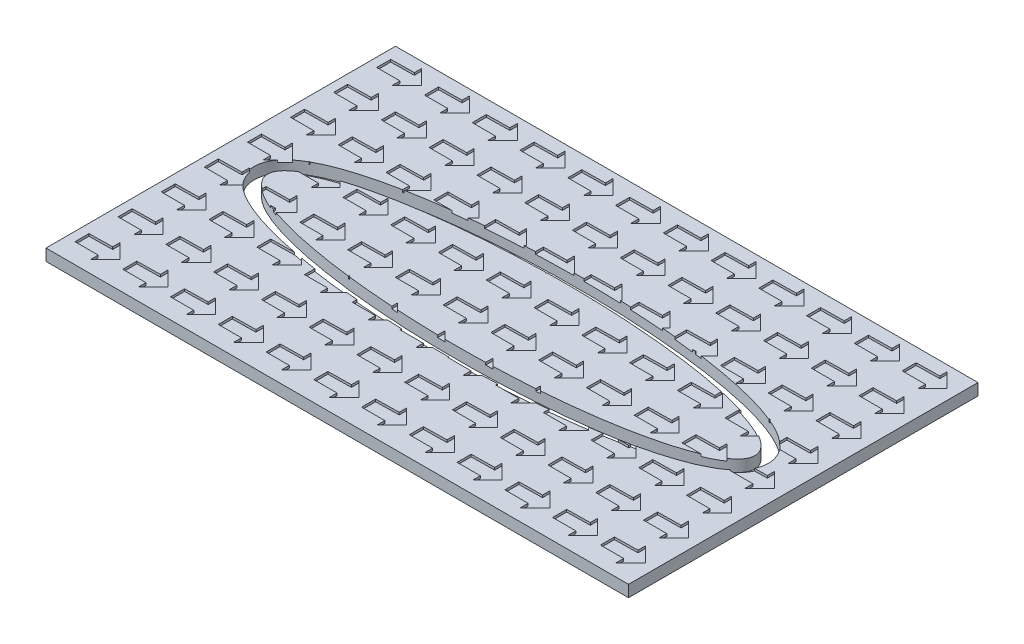
SolidWorks part; units mm, degrees
ref_plane "Front Plane" through (0, 0, 0) normal (0, 0, 1) x (1, 0, 0)
ref_plane "Top Plane" through (0, 0, 0) normal (0, 1, 0) x (1, 0, 0)
ref_plane "Right Plane" through (0, 0, 0) normal (1, 0, 0) x (0, 0, -1)
sketch "Sketch1" plane through (0, 0, 0) normal (0, 1, 0) x (1, 0, 0)
  line L1 (0, 0) -> (250, 0)
  line L2 (0, 0) -> (0, 150)
  line L3 (0, 150) -> (250, 150)
  line L4 (250, 0) -> (250, 150)
extrude "Boss-Extrude1" add sketch "Sketch1" along normal blind 5
sketch "Sketch2" plane through (0, 5, 0) normal (0, 1, 0) x (1, 0, 0)
  ellipse E0 centre (124.7013, 75) end of major axis (229.3097, 75) minor radius 23.3104
  spline S1 degree 3 poles (15.0926, 79.7899) (13.9648, 75) (15.0926, 70.2101) (17.6775, 66.4979) (21.0677, 63.529) (25.2033, 60.971) (30.1026, 58.6696) (37.6668, 55.8618) (49.0289, 52.785) (65.3757, 49.7981) (83.8897, 47.5943) (103.9101, 46.2414) (124.7013, 45.7853) (145.4926, 46.2414) (165.513, 47.5943) (184.027, 49.7981) (200.3738, 52.785) (211.7359, 55.8618) (219.3001, 58.6696) (224.1993, 60.971) (228.335, 63.529) (231.7252, 66.4979) (234.3101, 70.2101) (235.4379, 75) (234.3101, 79.7899) (231.7252, 83.5021) (228.335, 86.471) (224.1993, 89.029) (219.3001, 91.3304) (211.7359, 94.1382) (200.3738, 97.215) (184.027, 100.2019) (165.513, 102.4057) (145.4926, 103.7586) (124.7013, 104.2147) (103.9101, 103.7586) (83.8897, 102.4057) (65.3757, 100.2019) (49.0289, 97.215) (37.6668, 94.1382) (30.1026, 91.3304) (25.2033, 89.029) (21.0677, 86.471) (17.6775, 83.5021) (15.0926, 79.7899) (13.9648, 75) (15.0926, 70.2101) knots -0.294524 -0.19635 -0.098175 0 0.098175 0.19635 0.294524 0.392699 0.490874 0.589049 0.785398 0.981748 1.178097 1.374447 1.570796 1.767146 1.963495 2.159845 2.356194 2.552544 2.650719 2.748894 2.847068 2.945243 3.043418 3.141593 3.239767 3.337942 3.436117 3.534292 3.632467 3.730641 3.926991 4.12334 4.31969 4.516039 4.712389 4.908739 5.105088 5.301438 5.497787 5.694137 5.792311 5.890486 5.988661 6.086836 6.185011 6.283185 6.38136 6.479535 6.57771 only from (14.3407, 75) to (14.3407, 75)
extrude "Cut-Extrude1" cut sketch "Sketch2" against normal blind 5
sketch "Sketch3" plane through (0, 5, 0) normal (0, 1, 0) x (1, 0, 0)
  line L0 (3.8723, 144.0873) -> (3.8723, 138.0725)
  line L1 (3.8723, 138.0725) -> (13.8442, 138.0725)
  line L2 (13.8442, 138.0725) -> (13.8442, 134.7485)
  line L3 (13.8442, 134.7485) -> (20.1756, 141.0799)
  line L4 (20.1756, 141.0799) -> (13.8442, 147.4113)
  line L5 (13.8442, 147.4113) -> (13.8442, 144.2456)
  line L6 (13.8442, 144.2456) -> (3.8723, 144.0873)
  line L7 (24.3723, 144.0873) -> (24.3723, 138.0725)
  line L8 (24.3723, 138.0725) -> (34.3442, 138.0725)
  line L9 (34.3442, 138.0725) -> (34.3442, 134.7485)
  line L10 (34.3442, 134.7485) -> (40.6756, 141.0799)
  line L11 (40.6756, 141.0799) -> (34.3442, 147.4113)
  line L12 (34.3442, 147.4113) -> (34.3442, 144.2456)
  line L13 (34.3442, 144.2456) -> (24.3723, 144.0873)
  line L14 (44.8723, 144.0873) -> (44.8723, 138.0725)
  line L15 (44.8723, 138.0725) -> (54.8442, 138.0725)
  line L16 (54.8442, 138.0725) -> (54.8442, 134.7485)
  line L17 (54.8442, 134.7485) -> (61.1756, 141.0799)
  line L18 (61.1756, 141.0799) -> (54.8442, 147.4113)
  line L19 (54.8442, 147.4113) -> (54.8442, 144.2456)
  line L20 (54.8442, 144.2456) -> (44.8723, 144.0873)
  line L21 (65.3723, 144.0873) -> (65.3723, 138.0725)
  line L22 (65.3723, 138.0725) -> (75.3442, 138.0725)
  line L23 (75.3442, 138.0725) -> (75.3442, 134.7485)
  line L24 (75.3442, 134.7485) -> (81.6756, 141.0799)
  line L25 (81.6756, 141.0799) -> (75.3442, 147.4113)
  line L26 (75.3442, 147.4113) -> (75.3442, 144.2456)
  line L27 (75.3442, 144.2456) -> (65.3723, 144.0873)
  line L28 (85.8723, 144.0873) -> (85.8723, 138.0725)
  line L29 (85.8723, 138.0725) -> (95.8442, 138.0725)
  line L30 (95.8442, 138.0725) -> (95.8442, 134.7485)
  line L31 (95.8442, 134.7485) -> (102.1756, 141.0799)
  line L32 (102.1756, 141.0799) -> (95.8442, 147.4113)
  line L33 (95.8442, 147.4113) -> (95.8442, 144.2456)
  line L34 (95.8442, 144.2456) -> (85.8723, 144.0873)
  line L35 (106.3723, 144.0873) -> (106.3723, 138.0725)
  line L36 (106.3723, 138.0725) -> (116.3442, 138.0725)
  line L37 (116.3442, 138.0725) -> (116.3442, 134.7485)
  line L38 (116.3442, 134.7485) -> (122.6756, 141.0799)
  line L39 (122.6756, 141.0799) -> (116.3442, 147.4113)
  line L40 (116.3442, 147.4113) -> (116.3442, 144.2456)
  line L41 (116.3442, 144.2456) -> (106.3723, 144.0873)
  line L42 (126.8723, 144.0873) -> (126.8723, 138.0725)
  line L43 (126.8723, 138.0725) -> (136.8442, 138.0725)
  line L44 (136.8442, 138.0725) -> (136.8442, 134.7485)
  line L45 (136.8442, 134.7485) -> (143.1756, 141.0799)
  line L46 (143.1756, 141.0799) -> (136.8442, 147.4113)
  line L47 (136.8442, 147.4113) -> (136.8442, 144.2456)
  line L48 (136.8442, 144.2456) -> (126.8723, 144.0873)
  line L49 (147.3723, 144.0873) -> (147.3723, 138.0725)
  line L50 (147.3723, 138.0725) -> (157.3442, 138.0725)
  line L51 (157.3442, 138.0725) -> (157.3442, 134.7485)
  line L52 (157.3442, 134.7485) -> (163.6756, 141.0799)
  line L53 (163.6756, 141.0799) -> (157.3442, 147.4113)
  line L54 (157.3442, 147.4113) -> (157.3442, 144.2456)
  line L55 (157.3442, 144.2456) -> (147.3723, 144.0873)
  line L56 (167.8723, 144.0873) -> (167.8723, 138.0725)
  line L57 (167.8723, 138.0725) -> (177.8442, 138.0725)
  line L58 (177.8442, 138.0725) -> (177.8442, 134.7485)
  line L59 (177.8442, 134.7485) -> (184.1756, 141.0799)
  line L60 (184.1756, 141.0799) -> (177.8442, 147.4113)
  line L61 (177.8442, 147.4113) -> (177.8442, 144.2456)
  line L62 (177.8442, 144.2456) -> (167.8723, 144.0873)
  line L63 (188.3723, 144.0873) -> (188.3723, 138.0725)
  line L64 (188.3723, 138.0725) -> (198.3442, 138.0725)
  line L65 (198.3442, 138.0725) -> (198.3442, 134.7485)
  line L66 (198.3442, 134.7485) -> (204.6756, 141.0799)
  line L67 (204.6756, 141.0799) -> (198.3442, 147.4113)
  line L68 (198.3442, 147.4113) -> (198.3442, 144.2456)
  line L69 (198.3442, 144.2456) -> (188.3723, 144.0873)
  line L70 (208.8723, 144.0873) -> (208.8723, 138.0725)
  line L71 (208.8723, 138.0725) -> (218.8442, 138.0725)
  line L72 (218.8442, 138.0725) -> (218.8442, 134.7485)
  line L73 (218.8442, 134.7485) -> (225.1756, 141.0799)
  line L74 (225.1756, 141.0799) -> (218.8442, 147.4113)
  line L75 (218.8442, 147.4113) -> (218.8442, 144.2456)
  line L76 (218.8442, 144.2456) -> (208.8723, 144.0873)
  line L77 (229.3723, 144.0873) -> (229.3723, 138.0725)
  line L78 (229.3723, 138.0725) -> (239.3442, 138.0725)
  line L79 (239.3442, 138.0725) -> (239.3442, 134.7485)
  line L80 (239.3442, 134.7485) -> (245.6756, 141.0799)
  line L81 (245.6756, 141.0799) -> (239.3442, 147.4113)
  line L82 (239.3442, 147.4113) -> (239.3442, 144.2456)
  line L83 (239.3442, 144.2456) -> (229.3723, 144.0873)
  line L84 (24.3723, 125.5873) -> (24.3723, 119.5725)
  line L85 (24.3723, 119.5725) -> (34.3442, 119.5725)
  line L86 (34.3442, 119.5725) -> (34.3442, 116.2485)
  line L87 (34.3442, 116.2485) -> (40.6756, 122.5799)
  line L88 (40.6756, 122.5799) -> (34.3442, 128.9113)
  line L89 (34.3442, 128.9113) -> (34.3442, 125.7456)
  line L90 (34.3442, 125.7456) -> (24.3723, 125.5873)
  line L91 (44.8723, 125.5873) -> (44.8723, 119.5725)
  line L92 (44.8723, 119.5725) -> (54.8442, 119.5725)
  line L93 (54.8442, 119.5725) -> (54.8442, 116.2485)
  line L94 (54.8442, 116.2485) -> (61.1756, 122.5799)
  line L95 (61.1756, 122.5799) -> (54.8442, 128.9113)
  line L96 (54.8442, 128.9113) -> (54.8442, 125.7456)
  line L97 (54.8442, 125.7456) -> (44.8723, 125.5873)
  line L98 (65.3723, 125.5873) -> (65.3723, 119.5725)
  line L99 (65.3723, 119.5725) -> (75.3442, 119.5725)
  line L100 (75.3442, 119.5725) -> (75.3442, 116.2485)
  line L101 (75.3442, 116.2485) -> (81.6756, 122.5799)
  line L102 (81.6756, 122.5799) -> (75.3442, 128.9113)
  line L103 (75.3442, 128.9113) -> (75.3442, 125.7456)
  line L104 (75.3442, 125.7456) -> (65.3723, 125.5873)
  line L105 (85.8723, 125.5873) -> (85.8723, 119.5725)
  line L106 (85.8723, 119.5725) -> (95.8442, 119.5725)
  line L107 (95.8442, 119.5725) -> (95.8442, 116.2485)
  line L108 (95.8442, 116.2485) -> (102.1756, 122.5799)
  line L109 (102.1756, 122.5799) -> (95.8442, 128.9113)
  line L110 (95.8442, 128.9113) -> (95.8442, 125.7456)
  line L111 (95.8442, 125.7456) -> (85.8723, 125.5873)
  line L112 (106.3723, 125.5873) -> (106.3723, 119.5725)
  line L113 (106.3723, 119.5725) -> (116.3442, 119.5725)
  line L114 (116.3442, 119.5725) -> (116.3442, 116.2485)
  line L115 (116.3442, 116.2485) -> (122.6756, 122.5799)
  line L116 (122.6756, 122.5799) -> (116.3442, 128.9113)
  line L117 (116.3442, 128.9113) -> (116.3442, 125.7456)
  line L118 (116.3442, 125.7456) -> (106.3723, 125.5873)
  line L119 (126.8723, 125.5873) -> (126.8723, 119.5725)
  line L120 (126.8723, 119.5725) -> (136.8442, 119.5725)
  line L121 (136.8442, 119.5725) -> (136.8442, 116.2485)
  line L122 (136.8442, 116.2485) -> (143.1756, 122.5799)
  line L123 (143.1756, 122.5799) -> (136.8442, 128.9113)
  line L124 (136.8442, 128.9113) -> (136.8442, 125.7456)
  line L125 (136.8442, 125.7456) -> (126.8723, 125.5873)
  line L126 (147.3723, 125.5873) -> (147.3723, 119.5725)
  line L127 (147.3723, 119.5725) -> (157.3442, 119.5725)
  line L128 (157.3442, 119.5725) -> (157.3442, 116.2485)
  line L129 (157.3442, 116.2485) -> (163.6756, 122.5799)
  line L130 (163.6756, 122.5799) -> (157.3442, 128.9113)
  line L131 (157.3442, 128.9113) -> (157.3442, 125.7456)
  line L132 (157.3442, 125.7456) -> (147.3723, 125.5873)
  line L133 (167.8723, 125.5873) -> (167.8723, 119.5725)
  line L134 (167.8723, 119.5725) -> (177.8442, 119.5725)
  line L135 (177.8442, 119.5725) -> (177.8442, 116.2485)
  line L136 (177.8442, 116.2485) -> (184.1756, 122.5799)
  line L137 (184.1756, 122.5799) -> (177.8442, 128.9113)
  line L138 (177.8442, 128.9113) -> (177.8442, 125.7456)
  line L139 (177.8442, 125.7456) -> (167.8723, 125.5873)
  line L140 (188.3723, 125.5873) -> (188.3723, 119.5725)
  line L141 (188.3723, 119.5725) -> (198.3442, 119.5725)
  line L142 (198.3442, 119.5725) -> (198.3442, 116.2485)
  line L143 (198.3442, 116.2485) -> (204.6756, 122.5799)
  line L144 (204.6756, 122.5799) -> (198.3442, 128.9113)
  line L145 (198.3442, 128.9113) -> (198.3442, 125.7456)
  line L146 (198.3442, 125.7456) -> (188.3723, 125.5873)
  line L147 (208.8723, 125.5873) -> (208.8723, 119.5725)
  line L148 (208.8723, 119.5725) -> (218.8442, 119.5725)
  line L149 (218.8442, 119.5725) -> (218.8442, 116.2485)
  line L150 (218.8442, 116.2485) -> (225.1756, 122.5799)
  line L151 (225.1756, 122.5799) -> (218.8442, 128.9113)
  line L152 (218.8442, 128.9113) -> (218.8442, 125.7456)
  line L153 (218.8442, 125.7456) -> (208.8723, 125.5873)
  line L154 (229.3723, 125.5873) -> (229.3723, 119.5725)
  line L155 (229.3723, 119.5725) -> (239.3442, 119.5725)
  line L156 (239.3442, 119.5725) -> (239.3442, 116.2485)
  line L157 (239.3442, 116.2485) -> (245.6756, 122.5799)
  line L158 (245.6756, 122.5799) -> (239.3442, 128.9113)
  line L159 (239.3442, 128.9113) -> (239.3442, 125.7456)
  line L160 (239.3442, 125.7456) -> (229.3723, 125.5873)
  line L161 (24.3723, 107.0873) -> (24.3723, 101.0725)
  line L162 (24.3723, 101.0725) -> (34.3442, 101.0725)
  line L163 (34.3442, 101.0725) -> (34.3442, 97.7485)
  line L164 (34.3442, 97.7485) -> (40.6756, 104.0799)
  line L165 (40.6756, 104.0799) -> (34.3442, 110.4113)
  line L166 (34.3442, 110.4113) -> (34.3442, 107.2456)
  line L167 (34.3442, 107.2456) -> (24.3723, 107.0873)
  line L168 (44.8723, 107.0873) -> (44.8723, 101.0725)
  line L169 (44.8723, 101.0725) -> (54.8442, 101.0725)
  line L170 (54.8442, 101.0725) -> (54.8442, 97.7485)
  line L171 (54.8442, 97.7485) -> (61.1756, 104.0799)
  line L172 (61.1756, 104.0799) -> (54.8442, 110.4113)
  line L173 (54.8442, 110.4113) -> (54.8442, 107.2456)
  line L174 (54.8442, 107.2456) -> (44.8723, 107.0873)
  line L175 (65.3723, 107.0873) -> (65.3723, 101.0725)
  line L176 (65.3723, 101.0725) -> (75.3442, 101.0725)
  line L177 (75.3442, 101.0725) -> (75.3442, 97.7485)
  line L178 (75.3442, 97.7485) -> (81.6756, 104.0799)
  line L179 (81.6756, 104.0799) -> (75.3442, 110.4113)
  line L180 (75.3442, 110.4113) -> (75.3442, 107.2456)
  line L181 (75.3442, 107.2456) -> (65.3723, 107.0873)
  line L182 (85.8723, 107.0873) -> (85.8723, 101.0725)
  line L183 (85.8723, 101.0725) -> (95.8442, 101.0725)
  line L184 (95.8442, 101.0725) -> (95.8442, 97.7485)
  line L185 (95.8442, 97.7485) -> (102.1756, 104.0799)
  line L186 (102.1756, 104.0799) -> (95.8442, 110.4113)
  line L187 (95.8442, 110.4113) -> (95.8442, 107.2456)
  line L188 (95.8442, 107.2456) -> (85.8723, 107.0873)
  line L189 (106.3723, 107.0873) -> (106.3723, 101.0725)
  line L190 (106.3723, 101.0725) -> (116.3442, 101.0725)
  line L191 (116.3442, 101.0725) -> (116.3442, 97.7485)
  line L192 (116.3442, 97.7485) -> (122.6756, 104.0799)
  line L193 (122.6756, 104.0799) -> (116.3442, 110.4113)
  line L194 (116.3442, 110.4113) -> (116.3442, 107.2456)
  line L195 (116.3442, 107.2456) -> (106.3723, 107.0873)
  line L196 (126.8723, 107.0873) -> (126.8723, 101.0725)
  line L197 (126.8723, 101.0725) -> (136.8442, 101.0725)
  line L198 (136.8442, 101.0725) -> (136.8442, 97.7485)
  line L199 (136.8442, 97.7485) -> (143.1756, 104.0799)
  line L200 (143.1756, 104.0799) -> (136.8442, 110.4113)
  line L201 (136.8442, 110.4113) -> (136.8442, 107.2456)
  line L202 (136.8442, 107.2456) -> (126.8723, 107.0873)
  line L203 (147.3723, 107.0873) -> (147.3723, 101.0725)
  line L204 (147.3723, 101.0725) -> (157.3442, 101.0725)
  line L205 (157.3442, 101.0725) -> (157.3442, 97.7485)
  line L206 (157.3442, 97.7485) -> (163.6756, 104.0799)
  line L207 (163.6756, 104.0799) -> (157.3442, 110.4113)
  line L208 (157.3442, 110.4113) -> (157.3442, 107.2456)
  line L209 (157.3442, 107.2456) -> (147.3723, 107.0873)
  line L210 (167.8723, 107.0873) -> (167.8723, 101.0725)
  line L211 (167.8723, 101.0725) -> (177.8442, 101.0725)
  line L212 (177.8442, 101.0725) -> (177.8442, 97.7485)
  line L213 (177.8442, 97.7485) -> (184.1756, 104.0799)
  line L214 (184.1756, 104.0799) -> (177.8442, 110.4113)
  line L215 (177.8442, 110.4113) -> (177.8442, 107.2456)
  line L216 (177.8442, 107.2456) -> (167.8723, 107.0873)
  line L217 (188.3723, 107.0873) -> (188.3723, 101.0725)
  line L218 (188.3723, 101.0725) -> (198.3442, 101.0725)
  line L219 (198.3442, 101.0725) -> (198.3442, 97.7485)
  line L220 (198.3442, 97.7485) -> (204.6756, 104.0799)
  line L221 (204.6756, 104.0799) -> (198.3442, 110.4113)
  line L222 (198.3442, 110.4113) -> (198.3442, 107.2456)
  line L223 (198.3442, 107.2456) -> (188.3723, 107.0873)
  line L224 (208.8723, 107.0873) -> (208.8723, 101.0725)
  line L225 (208.8723, 101.0725) -> (218.8442, 101.0725)
  line L226 (218.8442, 101.0725) -> (218.8442, 97.7485)
  line L227 (218.8442, 97.7485) -> (225.1756, 104.0799)
  line L228 (225.1756, 104.0799) -> (218.8442, 110.4113)
  line L229 (218.8442, 110.4113) -> (218.8442, 107.2456)
  line L230 (218.8442, 107.2456) -> (208.8723, 107.0873)
  line L231 (229.3723, 107.0873) -> (229.3723, 101.0725)
  line L232 (229.3723, 101.0725) -> (239.3442, 101.0725)
  line L233 (239.3442, 101.0725) -> (239.3442, 97.7485)
  line L234 (239.3442, 97.7485) -> (245.6756, 104.0799)
  line L235 (245.6756, 104.0799) -> (239.3442, 110.4113)
  line L236 (239.3442, 110.4113) -> (239.3442, 107.2456)
  line L237 (239.3442, 107.2456) -> (229.3723, 107.0873)
  line L238 (24.3723, 88.5873) -> (24.3723, 82.5725)
  line L239 (24.3723, 82.5725) -> (34.3442, 82.5725)
  line L240 (34.3442, 82.5725) -> (34.3442, 79.2485)
  line L241 (34.3442, 79.2485) -> (40.6756, 85.5799)
  line L242 (40.6756, 85.5799) -> (34.3442, 91.9113)
  line L243 (34.3442, 91.9113) -> (34.3442, 88.7456)
  line L244 (34.3442, 88.7456) -> (24.3723, 88.5873)
  line L245 (44.8723, 88.5873) -> (44.8723, 82.5725)
  line L246 (44.8723, 82.5725) -> (54.8442, 82.5725)
  line L247 (54.8442, 82.5725) -> (54.8442, 79.2485)
  line L248 (54.8442, 79.2485) -> (61.1756, 85.5799)
  line L249 (61.1756, 85.5799) -> (54.8442, 91.9113)
  line L250 (54.8442, 91.9113) -> (54.8442, 88.7456)
  line L251 (54.8442, 88.7456) -> (44.8723, 88.5873)
  line L252 (65.3723, 88.5873) -> (65.3723, 82.5725)
  line L253 (65.3723, 82.5725) -> (75.3442, 82.5725)
  line L254 (75.3442, 82.5725) -> (75.3442, 79.2485)
  line L255 (75.3442, 79.2485) -> (81.6756, 85.5799)
  line L256 (81.6756, 85.5799) -> (75.3442, 91.9113)
  line L257 (75.3442, 91.9113) -> (75.3442, 88.7456)
  line L258 (75.3442, 88.7456) -> (65.3723, 88.5873)
  line L259 (85.8723, 88.5873) -> (85.8723, 82.5725)
  line L260 (85.8723, 82.5725) -> (95.8442, 82.5725)
  line L261 (95.8442, 82.5725) -> (95.8442, 79.2485)
  line L262 (95.8442, 79.2485) -> (102.1756, 85.5799)
  line L263 (102.1756, 85.5799) -> (95.8442, 91.9113)
  line L264 (95.8442, 91.9113) -> (95.8442, 88.7456)
  line L265 (95.8442, 88.7456) -> (85.8723, 88.5873)
  line L266 (106.3723, 88.5873) -> (106.3723, 82.5725)
  line L267 (106.3723, 82.5725) -> (116.3442, 82.5725)
  line L268 (116.3442, 82.5725) -> (116.3442, 79.2485)
  line L269 (116.3442, 79.2485) -> (122.6756, 85.5799)
  line L270 (122.6756, 85.5799) -> (116.3442, 91.9113)
  line L271 (116.3442, 91.9113) -> (116.3442, 88.7456)
  line L272 (116.3442, 88.7456) -> (106.3723, 88.5873)
  line L273 (126.8723, 88.5873) -> (126.8723, 82.5725)
  line L274 (126.8723, 82.5725) -> (136.8442, 82.5725)
  line L275 (136.8442, 82.5725) -> (136.8442, 79.2485)
  line L276 (136.8442, 79.2485) -> (143.1756, 85.5799)
  line L277 (143.1756, 85.5799) -> (136.8442, 91.9113)
  line L278 (136.8442, 91.9113) -> (136.8442, 88.7456)
  line L279 (136.8442, 88.7456) -> (126.8723, 88.5873)
  line L280 (147.3723, 88.5873) -> (147.3723, 82.5725)
  line L281 (147.3723, 82.5725) -> (157.3442, 82.5725)
  line L282 (157.3442, 82.5725) -> (157.3442, 79.2485)
  line L283 (157.3442, 79.2485) -> (163.6756, 85.5799)
  line L284 (163.6756, 85.5799) -> (157.3442, 91.9113)
  line L285 (157.3442, 91.9113) -> (157.3442, 88.7456)
  line L286 (157.3442, 88.7456) -> (147.3723, 88.5873)
  line L287 (167.8723, 88.5873) -> (167.8723, 82.5725)
  line L288 (167.8723, 82.5725) -> (177.8442, 82.5725)
  line L289 (177.8442, 82.5725) -> (177.8442, 79.2485)
  line L290 (177.8442, 79.2485) -> (184.1756, 85.5799)
  line L291 (184.1756, 85.5799) -> (177.8442, 91.9113)
  line L292 (177.8442, 91.9113) -> (177.8442, 88.7456)
  line L293 (177.8442, 88.7456) -> (167.8723, 88.5873)
  line L294 (188.3723, 88.5873) -> (188.3723, 82.5725)
  line L295 (188.3723, 82.5725) -> (198.3442, 82.5725)
  line L296 (198.3442, 82.5725) -> (198.3442, 79.2485)
  line L297 (198.3442, 79.2485) -> (204.6756, 85.5799)
  line L298 (204.6756, 85.5799) -> (198.3442, 91.9113)
  line L299 (198.3442, 91.9113) -> (198.3442, 88.7456)
  line L300 (198.3442, 88.7456) -> (188.3723, 88.5873)
  line L301 (208.8723, 88.5873) -> (208.8723, 82.5725)
  line L302 (208.8723, 82.5725) -> (218.8442, 82.5725)
  line L303 (218.8442, 82.5725) -> (218.8442, 79.2485)
  line L304 (218.8442, 79.2485) -> (225.1756, 85.5799)
  line L305 (225.1756, 85.5799) -> (218.8442, 91.9113)
  line L306 (218.8442, 91.9113) -> (218.8442, 88.7456)
  line L307 (218.8442, 88.7456) -> (208.8723, 88.5873)
  line L308 (229.3723, 88.5873) -> (229.3723, 82.5725)
  line L309 (229.3723, 82.5725) -> (239.3442, 82.5725)
  line L310 (239.3442, 82.5725) -> (239.3442, 79.2485)
  line L311 (239.3442, 79.2485) -> (245.6756, 85.5799)
  line L312 (245.6756, 85.5799) -> (239.3442, 91.9113)
  line L313 (239.3442, 91.9113) -> (239.3442, 88.7456)
  line L314 (239.3442, 88.7456) -> (229.3723, 88.5873)
  line L315 (24.3723, 70.0873) -> (24.3723, 64.0725)
  line L316 (24.3723, 64.0725) -> (34.3442, 64.0725)
  line L317 (34.3442, 64.0725) -> (34.3442, 60.7485)
  line L318 (34.3442, 60.7485) -> (40.6756, 67.0799)
  line L319 (40.6756, 67.0799) -> (34.3442, 73.4113)
  line L320 (34.3442, 73.4113) -> (34.3442, 70.2456)
  line L321 (34.3442, 70.2456) -> (24.3723, 70.0873)
  line L322 (44.8723, 70.0873) -> (44.8723, 64.0725)
  line L323 (44.8723, 64.0725) -> (54.8442, 64.0725)
  line L324 (54.8442, 64.0725) -> (54.8442, 60.7485)
  line L325 (54.8442, 60.7485) -> (61.1756, 67.0799)
  line L326 (61.1756, 67.0799) -> (54.8442, 73.4113)
  line L327 (54.8442, 73.4113) -> (54.8442, 70.2456)
  line L328 (54.8442, 70.2456) -> (44.8723, 70.0873)
  line L329 (65.3723, 70.0873) -> (65.3723, 64.0725)
  line L330 (65.3723, 64.0725) -> (75.3442, 64.0725)
  line L331 (75.3442, 64.0725) -> (75.3442, 60.7485)
  line L332 (75.3442, 60.7485) -> (81.6756, 67.0799)
  line L333 (81.6756, 67.0799) -> (75.3442, 73.4113)
  line L334 (75.3442, 73.4113) -> (75.3442, 70.2456)
  line L335 (75.3442, 70.2456) -> (65.3723, 70.0873)
  line L336 (85.8723, 70.0873) -> (85.8723, 64.0725)
  line L337 (85.8723, 64.0725) -> (95.8442, 64.0725)
  line L338 (95.8442, 64.0725) -> (95.8442, 60.7485)
  line L339 (95.8442, 60.7485) -> (102.1756, 67.0799)
  line L340 (102.1756, 67.0799) -> (95.8442, 73.4113)
  line L341 (95.8442, 73.4113) -> (95.8442, 70.2456)
  line L342 (95.8442, 70.2456) -> (85.8723, 70.0873)
  line L343 (106.3723, 70.0873) -> (106.3723, 64.0725)
  line L344 (106.3723, 64.0725) -> (116.3442, 64.0725)
  line L345 (116.3442, 64.0725) -> (116.3442, 60.7485)
  line L346 (116.3442, 60.7485) -> (122.6756, 67.0799)
  line L347 (122.6756, 67.0799) -> (116.3442, 73.4113)
  line L348 (116.3442, 73.4113) -> (116.3442, 70.2456)
  line L349 (116.3442, 70.2456) -> (106.3723, 70.0873)
  line L350 (126.8723, 70.0873) -> (126.8723, 64.0725)
  line L351 (126.8723, 64.0725) -> (136.8442, 64.0725)
  line L352 (136.8442, 64.0725) -> (136.8442, 60.7485)
  line L353 (136.8442, 60.7485) -> (143.1756, 67.0799)
  line L354 (143.1756, 67.0799) -> (136.8442, 73.4113)
  line L355 (136.8442, 73.4113) -> (136.8442, 70.2456)
  line L356 (136.8442, 70.2456) -> (126.8723, 70.0873)
  line L357 (147.3723, 70.0873) -> (147.3723, 64.0725)
  line L358 (147.3723, 64.0725) -> (157.3442, 64.0725)
  line L359 (157.3442, 64.0725) -> (157.3442, 60.7485)
  line L360 (157.3442, 60.7485) -> (163.6756, 67.0799)
  line L361 (163.6756, 67.0799) -> (157.3442, 73.4113)
  line L362 (157.3442, 73.4113) -> (157.3442, 70.2456)
  line L363 (157.3442, 70.2456) -> (147.3723, 70.0873)
  line L364 (167.8723, 70.0873) -> (167.8723, 64.0725)
  line L365 (167.8723, 64.0725) -> (177.8442, 64.0725)
  line L366 (177.8442, 64.0725) -> (177.8442, 60.7485)
  line L367 (177.8442, 60.7485) -> (184.1756, 67.0799)
  line L368 (184.1756, 67.0799) -> (177.8442, 73.4113)
  line L369 (177.8442, 73.4113) -> (177.8442, 70.2456)
  line L370 (177.8442, 70.2456) -> (167.8723, 70.0873)
  line L371 (188.3723, 70.0873) -> (188.3723, 64.0725)
  line L372 (188.3723, 64.0725) -> (198.3442, 64.0725)
  line L373 (198.3442, 64.0725) -> (198.3442, 60.7485)
  line L374 (198.3442, 60.7485) -> (204.6756, 67.0799)
  line L375 (204.6756, 67.0799) -> (198.3442, 73.4113)
  line L376 (198.3442, 73.4113) -> (198.3442, 70.2456)
  line L377 (198.3442, 70.2456) -> (188.3723, 70.0873)
  line L378 (208.8723, 70.0873) -> (208.8723, 64.0725)
  line L379 (208.8723, 64.0725) -> (218.8442, 64.0725)
  line L380 (218.8442, 64.0725) -> (218.8442, 60.7485)
  line L381 (218.8442, 60.7485) -> (225.1756, 67.0799)
  line L382 (225.1756, 67.0799) -> (218.8442, 73.4113)
  line L383 (218.8442, 73.4113) -> (218.8442, 70.2456)
  line L384 (218.8442, 70.2456) -> (208.8723, 70.0873)
  line L385 (229.3723, 70.0873) -> (229.3723, 64.0725)
  line L386 (229.3723, 64.0725) -> (239.3442, 64.0725)
  line L387 (239.3442, 64.0725) -> (239.3442, 60.7485)
  line L388 (239.3442, 60.7485) -> (245.6756, 67.0799)
  line L389 (245.6756, 67.0799) -> (239.3442, 73.4113)
  line L390 (239.3442, 73.4113) -> (239.3442, 70.2456)
  line L391 (239.3442, 70.2456) -> (229.3723, 70.0873)
  line L392 (24.3723, 51.5873) -> (24.3723, 45.5725)
  line L393 (24.3723, 45.5725) -> (34.3442, 45.5725)
  line L394 (34.3442, 45.5725) -> (34.3442, 42.2485)
  line L395 (34.3442, 42.2485) -> (40.6756, 48.5799)
  line L396 (40.6756, 48.5799) -> (34.3442, 54.9113)
  line L397 (34.3442, 54.9113) -> (34.3442, 51.7456)
  line L398 (34.3442, 51.7456) -> (24.3723, 51.5873)
  line L399 (44.8723, 51.5873) -> (44.8723, 45.5725)
  line L400 (44.8723, 45.5725) -> (54.8442, 45.5725)
  line L401 (54.8442, 45.5725) -> (54.8442, 42.2485)
  line L402 (54.8442, 42.2485) -> (61.1756, 48.5799)
  line L403 (61.1756, 48.5799) -> (54.8442, 54.9113)
  line L404 (54.8442, 54.9113) -> (54.8442, 51.7456)
  line L405 (54.8442, 51.7456) -> (44.8723, 51.5873)
  line L406 (65.3723, 51.5873) -> (65.3723, 45.5725)
  line L407 (65.3723, 45.5725) -> (75.3442, 45.5725)
  line L408 (75.3442, 45.5725) -> (75.3442, 42.2485)
  line L409 (75.3442, 42.2485) -> (81.6756, 48.5799)
  line L410 (81.6756, 48.5799) -> (75.3442, 54.9113)
  line L411 (75.3442, 54.9113) -> (75.3442, 51.7456)
  line L412 (75.3442, 51.7456) -> (65.3723, 51.5873)
  line L413 (85.8723, 51.5873) -> (85.8723, 45.5725)
  line L414 (85.8723, 45.5725) -> (95.8442, 45.5725)
  line L415 (95.8442, 45.5725) -> (95.8442, 42.2485)
  line L416 (95.8442, 42.2485) -> (102.1756, 48.5799)
  line L417 (102.1756, 48.5799) -> (95.8442, 54.9113)
  line L418 (95.8442, 54.9113) -> (95.8442, 51.7456)
  line L419 (95.8442, 51.7456) -> (85.8723, 51.5873)
  line L420 (106.3723, 51.5873) -> (106.3723, 45.5725)
  line L421 (106.3723, 45.5725) -> (116.3442, 45.5725)
  line L422 (116.3442, 45.5725) -> (116.3442, 42.2485)
  line L423 (116.3442, 42.2485) -> (122.6756, 48.5799)
  line L424 (122.6756, 48.5799) -> (116.3442, 54.9113)
  line L425 (116.3442, 54.9113) -> (116.3442, 51.7456)
  line L426 (116.3442, 51.7456) -> (106.3723, 51.5873)
  line L427 (126.8723, 51.5873) -> (126.8723, 45.5725)
  line L428 (126.8723, 45.5725) -> (136.8442, 45.5725)
  line L429 (136.8442, 45.5725) -> (136.8442, 42.2485)
  line L430 (136.8442, 42.2485) -> (143.1756, 48.5799)
  line L431 (143.1756, 48.5799) -> (136.8442, 54.9113)
  line L432 (136.8442, 54.9113) -> (136.8442, 51.7456)
  line L433 (136.8442, 51.7456) -> (126.8723, 51.5873)
  line L434 (147.3723, 51.5873) -> (147.3723, 45.5725)
  line L435 (147.3723, 45.5725) -> (157.3442, 45.5725)
  line L436 (157.3442, 45.5725) -> (157.3442, 42.2485)
  line L437 (157.3442, 42.2485) -> (163.6756, 48.5799)
  line L438 (163.6756, 48.5799) -> (157.3442, 54.9113)
  line L439 (157.3442, 54.9113) -> (157.3442, 51.7456)
  line L440 (157.3442, 51.7456) -> (147.3723, 51.5873)
  line L441 (167.8723, 51.5873) -> (167.8723, 45.5725)
  line L442 (167.8723, 45.5725) -> (177.8442, 45.5725)
  line L443 (177.8442, 45.5725) -> (177.8442, 42.2485)
  line L444 (177.8442, 42.2485) -> (184.1756, 48.5799)
  line L445 (184.1756, 48.5799) -> (177.8442, 54.9113)
  line L446 (177.8442, 54.9113) -> (177.8442, 51.7456)
  line L447 (177.8442, 51.7456) -> (167.8723, 51.5873)
  line L448 (188.3723, 51.5873) -> (188.3723, 45.5725)
  line L449 (188.3723, 45.5725) -> (198.3442, 45.5725)
  line L450 (198.3442, 45.5725) -> (198.3442, 42.2485)
  line L451 (198.3442, 42.2485) -> (204.6756, 48.5799)
  line L452 (204.6756, 48.5799) -> (198.3442, 54.9113)
  line L453 (198.3442, 54.9113) -> (198.3442, 51.7456)
  line L454 (198.3442, 51.7456) -> (188.3723, 51.5873)
  line L455 (208.8723, 51.5873) -> (208.8723, 45.5725)
  line L456 (208.8723, 45.5725) -> (218.8442, 45.5725)
  line L457 (218.8442, 45.5725) -> (218.8442, 42.2485)
  line L458 (218.8442, 42.2485) -> (225.1756, 48.5799)
  line L459 (225.1756, 48.5799) -> (218.8442, 54.9113)
  line L460 (218.8442, 54.9113) -> (218.8442, 51.7456)
  line L461 (218.8442, 51.7456) -> (208.8723, 51.5873)
  line L462 (229.3723, 51.5873) -> (229.3723, 45.5725)
  line L463 (229.3723, 45.5725) -> (239.3442, 45.5725)
  line L464 (239.3442, 45.5725) -> (239.3442, 42.2485)
  line L465 (239.3442, 42.2485) -> (245.6756, 48.5799)
  line L466 (245.6756, 48.5799) -> (239.3442, 54.9113)
  line L467 (239.3442, 54.9113) -> (239.3442, 51.7456)
  line L468 (239.3442, 51.7456) -> (229.3723, 51.5873)
  line L469 (24.3723, 33.0873) -> (24.3723, 27.0725)
  line L470 (24.3723, 27.0725) -> (34.3442, 27.0725)
  line L471 (34.3442, 27.0725) -> (34.3442, 23.7485)
  line L472 (34.3442, 23.7485) -> (40.6756, 30.0799)
  line L473 (40.6756, 30.0799) -> (34.3442, 36.4113)
  line L474 (34.3442, 36.4113) -> (34.3442, 33.2456)
  line L475 (34.3442, 33.2456) -> (24.3723, 33.0873)
  line L476 (44.8723, 33.0873) -> (44.8723, 27.0725)
  line L477 (44.8723, 27.0725) -> (54.8442, 27.0725)
  line L478 (54.8442, 27.0725) -> (54.8442, 23.7485)
  line L479 (54.8442, 23.7485) -> (61.1756, 30.0799)
  line L480 (61.1756, 30.0799) -> (54.8442, 36.4113)
  line L481 (54.8442, 36.4113) -> (54.8442, 33.2456)
  line L482 (54.8442, 33.2456) -> (44.8723, 33.0873)
  line L483 (65.3723, 33.0873) -> (65.3723, 27.0725)
  line L484 (65.3723, 27.0725) -> (75.3442, 27.0725)
  line L485 (75.3442, 27.0725) -> (75.3442, 23.7485)
  line L486 (75.3442, 23.7485) -> (81.6756, 30.0799)
  line L487 (81.6756, 30.0799) -> (75.3442, 36.4113)
  line L488 (75.3442, 36.4113) -> (75.3442, 33.2456)
  line L489 (75.3442, 33.2456) -> (65.3723, 33.0873)
  line L490 (85.8723, 33.0873) -> (85.8723, 27.0725)
  line L491 (85.8723, 27.0725) -> (95.8442, 27.0725)
  line L492 (95.8442, 27.0725) -> (95.8442, 23.7485)
  line L493 (95.8442, 23.7485) -> (102.1756, 30.0799)
  line L494 (102.1756, 30.0799) -> (95.8442, 36.4113)
  line L495 (95.8442, 36.4113) -> (95.8442, 33.2456)
  line L496 (95.8442, 33.2456) -> (85.8723, 33.0873)
  line L497 (106.3723, 33.0873) -> (106.3723, 27.0725)
  line L498 (106.3723, 27.0725) -> (116.3442, 27.0725)
  line L499 (116.3442, 27.0725) -> (116.3442, 23.7485)
  line L500 (116.3442, 23.7485) -> (122.6756, 30.0799)
  line L501 (122.6756, 30.0799) -> (116.3442, 36.4113)
  line L502 (116.3442, 36.4113) -> (116.3442, 33.2456)
  line L503 (116.3442, 33.2456) -> (106.3723, 33.0873)
  line L504 (126.8723, 33.0873) -> (126.8723, 27.0725)
  line L505 (126.8723, 27.0725) -> (136.8442, 27.0725)
  line L506 (136.8442, 27.0725) -> (136.8442, 23.7485)
  line L507 (136.8442, 23.7485) -> (143.1756, 30.0799)
  line L508 (143.1756, 30.0799) -> (136.8442, 36.4113)
  line L509 (136.8442, 36.4113) -> (136.8442, 33.2456)
  line L510 (136.8442, 33.2456) -> (126.8723, 33.0873)
  line L511 (147.3723, 33.0873) -> (147.3723, 27.0725)
  line L512 (147.3723, 27.0725) -> (157.3442, 27.0725)
  line L513 (157.3442, 27.0725) -> (157.3442, 23.7485)
  line L514 (157.3442, 23.7485) -> (163.6756, 30.0799)
  line L515 (163.6756, 30.0799) -> (157.3442, 36.4113)
  line L516 (157.3442, 36.4113) -> (157.3442, 33.2456)
  line L517 (157.3442, 33.2456) -> (147.3723, 33.0873)
  line L518 (167.8723, 33.0873) -> (167.8723, 27.0725)
  line L519 (167.8723, 27.0725) -> (177.8442, 27.0725)
  line L520 (177.8442, 27.0725) -> (177.8442, 23.7485)
  line L521 (177.8442, 23.7485) -> (184.1756, 30.0799)
  line L522 (184.1756, 30.0799) -> (177.8442, 36.4113)
  line L523 (177.8442, 36.4113) -> (177.8442, 33.2456)
  line L524 (177.8442, 33.2456) -> (167.8723, 33.0873)
  line L525 (188.3723, 33.0873) -> (188.3723, 27.0725)
  line L526 (188.3723, 27.0725) -> (198.3442, 27.0725)
  line L527 (198.3442, 27.0725) -> (198.3442, 23.7485)
  line L528 (198.3442, 23.7485) -> (204.6756, 30.0799)
  line L529 (204.6756, 30.0799) -> (198.3442, 36.4113)
  line L530 (198.3442, 36.4113) -> (198.3442, 33.2456)
  line L531 (198.3442, 33.2456) -> (188.3723, 33.0873)
  line L532 (208.8723, 33.0873) -> (208.8723, 27.0725)
  line L533 (208.8723, 27.0725) -> (218.8442, 27.0725)
  line L534 (218.8442, 27.0725) -> (218.8442, 23.7485)
  line L535 (218.8442, 23.7485) -> (225.1756, 30.0799)
  line L536 (225.1756, 30.0799) -> (218.8442, 36.4113)
  line L537 (218.8442, 36.4113) -> (218.8442, 33.2456)
  line L538 (218.8442, 33.2456) -> (208.8723, 33.0873)
  line L539 (229.3723, 33.0873) -> (229.3723, 27.0725)
  line L540 (229.3723, 27.0725) -> (239.3442, 27.0725)
  line L541 (239.3442, 27.0725) -> (239.3442, 23.7485)
  line L542 (239.3442, 23.7485) -> (245.6756, 30.0799)
  line L543 (245.6756, 30.0799) -> (239.3442, 36.4113)
  line L544 (239.3442, 36.4113) -> (239.3442, 33.2456)
  line L545 (239.3442, 33.2456) -> (229.3723, 33.0873)
  line L546 (24.3723, 14.5873) -> (24.3723, 8.5725)
  line L547 (24.3723, 8.5725) -> (34.3442, 8.5725)
  line L548 (34.3442, 8.5725) -> (34.3442, 5.2485)
  line L549 (34.3442, 5.2485) -> (40.6756, 11.5799)
  line L550 (40.6756, 11.5799) -> (34.3442, 17.9113)
  line L551 (34.3442, 17.9113) -> (34.3442, 14.7456)
  line L552 (34.3442, 14.7456) -> (24.3723, 14.5873)
  line L553 (44.8723, 14.5873) -> (44.8723, 8.5725)
  line L554 (44.8723, 8.5725) -> (54.8442, 8.5725)
  line L555 (54.8442, 8.5725) -> (54.8442, 5.2485)
  line L556 (54.8442, 5.2485) -> (61.1756, 11.5799)
  line L557 (61.1756, 11.5799) -> (54.8442, 17.9113)
  line L558 (54.8442, 17.9113) -> (54.8442, 14.7456)
  line L559 (54.8442, 14.7456) -> (44.8723, 14.5873)
  line L560 (65.3723, 14.5873) -> (65.3723, 8.5725)
  line L561 (65.3723, 8.5725) -> (75.3442, 8.5725)
  line L562 (75.3442, 8.5725) -> (75.3442, 5.2485)
  line L563 (75.3442, 5.2485) -> (81.6756, 11.5799)
  line L564 (81.6756, 11.5799) -> (75.3442, 17.9113)
  line L565 (75.3442, 17.9113) -> (75.3442, 14.7456)
  line L566 (75.3442, 14.7456) -> (65.3723, 14.5873)
  line L567 (85.8723, 14.5873) -> (85.8723, 8.5725)
  line L568 (85.8723, 8.5725) -> (95.8442, 8.5725)
  line L569 (95.8442, 8.5725) -> (95.8442, 5.2485)
  line L570 (95.8442, 5.2485) -> (102.1756, 11.5799)
  line L571 (102.1756, 11.5799) -> (95.8442, 17.9113)
  line L572 (95.8442, 17.9113) -> (95.8442, 14.7456)
  line L573 (95.8442, 14.7456) -> (85.8723, 14.5873)
  line L574 (106.3723, 14.5873) -> (106.3723, 8.5725)
  line L575 (106.3723, 8.5725) -> (116.3442, 8.5725)
  line L576 (116.3442, 8.5725) -> (116.3442, 5.2485)
  line L577 (116.3442, 5.2485) -> (122.6756, 11.5799)
  line L578 (122.6756, 11.5799) -> (116.3442, 17.9113)
  line L579 (116.3442, 17.9113) -> (116.3442, 14.7456)
  line L580 (116.3442, 14.7456) -> (106.3723, 14.5873)
  line L581 (126.8723, 14.5873) -> (126.8723, 8.5725)
  line L582 (126.8723, 8.5725) -> (136.8442, 8.5725)
  line L583 (136.8442, 8.5725) -> (136.8442, 5.2485)
  line L584 (136.8442, 5.2485) -> (143.1756, 11.5799)
  line L585 (143.1756, 11.5799) -> (136.8442, 17.9113)
  line L586 (136.8442, 17.9113) -> (136.8442, 14.7456)
  line L587 (136.8442, 14.7456) -> (126.8723, 14.5873)
  line L588 (147.3723, 14.5873) -> (147.3723, 8.5725)
  line L589 (147.3723, 8.5725) -> (157.3442, 8.5725)
  line L590 (157.3442, 8.5725) -> (157.3442, 5.2485)
  line L591 (157.3442, 5.2485) -> (163.6756, 11.5799)
  line L592 (163.6756, 11.5799) -> (157.3442, 17.9113)
  line L593 (157.3442, 17.9113) -> (157.3442, 14.7456)
  line L594 (157.3442, 14.7456) -> (147.3723, 14.5873)
  line L595 (167.8723, 14.5873) -> (167.8723, 8.5725)
  line L596 (167.8723, 8.5725) -> (177.8442, 8.5725)
  line L597 (177.8442, 8.5725) -> (177.8442, 5.2485)
  line L598 (177.8442, 5.2485) -> (184.1756, 11.5799)
  line L599 (184.1756, 11.5799) -> (177.8442, 17.9113)
  line L600 (177.8442, 17.9113) -> (177.8442, 14.7456)
  line L601 (177.8442, 14.7456) -> (167.8723, 14.5873)
  line L602 (188.3723, 14.5873) -> (188.3723, 8.5725)
  line L603 (188.3723, 8.5725) -> (198.3442, 8.5725)
  line L604 (198.3442, 8.5725) -> (198.3442, 5.2485)
  line L605 (198.3442, 5.2485) -> (204.6756, 11.5799)
  line L606 (204.6756, 11.5799) -> (198.3442, 17.9113)
  line L607 (198.3442, 17.9113) -> (198.3442, 14.7456)
  line L608 (198.3442, 14.7456) -> (188.3723, 14.5873)
  line L609 (208.8723, 14.5873) -> (208.8723, 8.5725)
  line L610 (208.8723, 8.5725) -> (218.8442, 8.5725)
  line L611 (218.8442, 8.5725) -> (218.8442, 5.2485)
  line L612 (218.8442, 5.2485) -> (225.1756, 11.5799)
  line L613 (225.1756, 11.5799) -> (218.8442, 17.9113)
  line L614 (218.8442, 17.9113) -> (218.8442, 14.7456)
  line L615 (218.8442, 14.7456) -> (208.8723, 14.5873)
  line L616 (229.3723, 14.5873) -> (229.3723, 8.5725)
  line L617 (229.3723, 8.5725) -> (239.3442, 8.5725)
  line L618 (239.3442, 8.5725) -> (239.3442, 5.2485)
  line L619 (239.3442, 5.2485) -> (245.6756, 11.5799)
  line L620 (245.6756, 11.5799) -> (239.3442, 17.9113)
  line L621 (239.3442, 17.9113) -> (239.3442, 14.7456)
  line L622 (239.3442, 14.7456) -> (229.3723, 14.5873)
  line L623 (3.8723, 125.5873) -> (3.8723, 119.5725)
  line L624 (3.8723, 119.5725) -> (13.8442, 119.5725)
  line L625 (13.8442, 119.5725) -> (13.8442, 116.2485)
  line L626 (13.8442, 116.2485) -> (20.1756, 122.5799)
  line L627 (20.1756, 122.5799) -> (13.8442, 128.9113)
  line L628 (13.8442, 128.9113) -> (13.8442, 125.7456)
  line L629 (13.8442, 125.7456) -> (3.8723, 125.5873)
  line L630 (3.8723, 107.0873) -> (3.8723, 101.0725)
  line L631 (3.8723, 101.0725) -> (13.8442, 101.0725)
  line L632 (13.8442, 101.0725) -> (13.8442, 97.7485)
  line L633 (13.8442, 97.7485) -> (20.1756, 104.0799)
  line L634 (20.1756, 104.0799) -> (13.8442, 110.4113)
  line L635 (13.8442, 110.4113) -> (13.8442, 107.2456)
  line L636 (13.8442, 107.2456) -> (3.8723, 107.0873)
  line L637 (3.8723, 88.5873) -> (3.8723, 82.5725)
  line L638 (3.8723, 82.5725) -> (13.8442, 82.5725)
  line L639 (13.8442, 82.5725) -> (13.8442, 79.2485)
  line L640 (13.8442, 79.2485) -> (20.1756, 85.5799)
  line L641 (20.1756, 85.5799) -> (13.8442, 91.9113)
  line L642 (13.8442, 91.9113) -> (13.8442, 88.7456)
  line L643 (13.8442, 88.7456) -> (3.8723, 88.5873)
  line L644 (3.8723, 70.0873) -> (3.8723, 64.0725)
  line L645 (3.8723, 64.0725) -> (13.8442, 64.0725)
  line L646 (13.8442, 64.0725) -> (13.8442, 60.7485)
  line L647 (13.8442, 60.7485) -> (20.1756, 67.0799)
  line L648 (20.1756, 67.0799) -> (13.8442, 73.4113)
  line L649 (13.8442, 73.4113) -> (13.8442, 70.2456)
  line L650 (13.8442, 70.2456) -> (3.8723, 70.0873)
  line L651 (3.8723, 51.5873) -> (3.8723, 45.5725)
  line L652 (3.8723, 45.5725) -> (13.8442, 45.5725)
  line L653 (13.8442, 45.5725) -> (13.8442, 42.2485)
  line L654 (13.8442, 42.2485) -> (20.1756, 48.5799)
  line L655 (20.1756, 48.5799) -> (13.8442, 54.9113)
  line L656 (13.8442, 54.9113) -> (13.8442, 51.7456)
  line L657 (13.8442, 51.7456) -> (3.8723, 51.5873)
  line L658 (3.8723, 33.0873) -> (3.8723, 27.0725)
  line L659 (3.8723, 27.0725) -> (13.8442, 27.0725)
  line L660 (13.8442, 27.0725) -> (13.8442, 23.7485)
  line L661 (13.8442, 23.7485) -> (20.1756, 30.0799)
  line L662 (20.1756, 30.0799) -> (13.8442, 36.4113)
  line L663 (13.8442, 36.4113) -> (13.8442, 33.2456)
  line L664 (13.8442, 33.2456) -> (3.8723, 33.0873)
  line L665 (3.8723, 14.5873) -> (3.8723, 8.5725)
  line L666 (3.8723, 8.5725) -> (13.8442, 8.5725)
  line L667 (13.8442, 8.5725) -> (13.8442, 5.2485)
  line L668 (13.8442, 5.2485) -> (20.1756, 11.5799)
  line L669 (20.1756, 11.5799) -> (13.8442, 17.9113)
  line L670 (13.8442, 17.9113) -> (13.8442, 14.7456)
  line L671 (13.8442, 14.7456) -> (3.8723, 14.5873)
  dimension "D1" = 12
  dimension "D2" = 8
extrude "Cut-Extrude2" cut sketch "Sketch3" against normal blind 1
